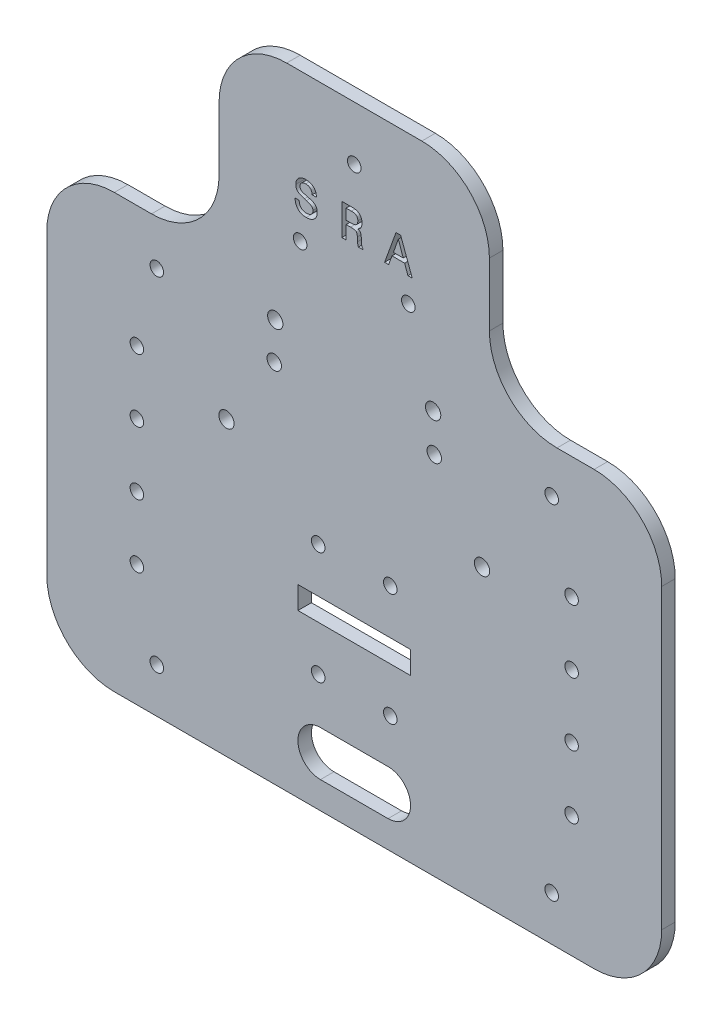
SolidWorks part; units mm, degrees
material "Acrylic (Medium-high impact)"
ref_plane "Front Plane" through (0, 0, 0) normal (0, 0, 1) x (1, 0, 0)
ref_plane "Top Plane" through (0, 0, 0) normal (0, 1, 0) x (1, 0, 0)
ref_plane "Right Plane" through (0, 0, 0) normal (1, 0, 0) x (0, 0, -1)
sketch "Model" plane through (0, 0, 0) normal (0, 0, 1) x (1, 0, 0)
  line L0 (906.1946, 1084.1431) -> (906.1946, 1018.1431)
  line L1 (891.1946, 1003.1431) -> (784.6946, 1003.1431)
  line L2 (845.4446, 1019.1431) -> (830.4446, 1019.1431)
  line L3 (845.4446, 1009.1431) -> (830.4446, 1009.1431)
  line L4 (769.6946, 1084.1431) -> (769.6946, 1018.1431)
  line L5 (891.1946, 1099.1431) -> (882.9446, 1099.1431)
  line L6 (784.6946, 1099.1431) -> (792.9446, 1099.1431)
  line L319 (837.9446, 1143.1431) -> (852.9446, 1143.1431)
  line L320 (837.9446, 1143.1431) -> (852.9446, 1143.1431)
  line L321 (867.9446, 1128.1431) -> (867.9446, 1114.1431)
  line L322 (837.9446, 1143.1431) -> (822.9446, 1143.1431)
  line L323 (807.9446, 1128.1431) -> (807.9446, 1114.1431)
  line L324 (825.4446, 1039.1431) -> (825.4446, 1044.1431)
  line L325 (825.4446, 1044.1431) -> (850.4446, 1044.1431)
  line L326 (850.4446, 1044.1431) -> (850.4446, 1039.1431)
  line L327 (850.4446, 1039.1431) -> (825.4446, 1039.1431)
  circle A0 centre (881.7696, 1013.0631) radius 1.5
  circle A1 centre (794.1196, 1013.0631) radius 1.5
  circle A2 centre (886.1946, 1058.1431) radius 1.5
  circle A3 centre (886.1946, 1044.1431) radius 1.5
  circle A4 centre (789.6946, 1058.1431) radius 1.5
  circle A5 centre (789.6946, 1044.1431) radius 1.5
  circle A6 centre (825.9446, 1110.3585) radius 1.5
  circle A7 centre (849.9446, 1110.3585) radius 1.5
  circle A8 centre (837.9446, 1131.1431) radius 1.5
  circle A9 centre (829.9446, 1054.1431) radius 1.5
  circle A10 centre (845.9446, 1054.1431) radius 1.5
  arc A11 (891.1946, 1003.1431) -> (906.1946, 1018.1431) centre (891.1946, 1018.1431) ccw
  arc A12 (769.6946, 1018.1431) -> (784.6946, 1003.1431) centre (784.6946, 1018.1431) ccw
  arc A13 (850.4446, 1014.1431) -> (845.4446, 1019.1431) centre (845.4446, 1014.1431) ccw
  arc A14 (830.4446, 1019.1431) -> (825.4446, 1014.1431) centre (830.4446, 1014.1431) ccw
  arc A15 (845.4446, 1009.1431) -> (850.4446, 1014.1431) centre (845.4446, 1014.1431) ccw
  arc A16 (825.4446, 1014.1431) -> (830.4446, 1009.1431) centre (830.4446, 1014.1431) ccw
  arc A17 (906.1946, 1084.1431) -> (891.1946, 1099.1431) centre (891.1946, 1084.1431) ccw
  arc A18 (784.6946, 1099.1431) -> (769.6946, 1084.1431) centre (784.6946, 1084.1431) ccw
  arc A19 (867.9446, 1114.1431) -> (882.9446, 1099.1431) centre (882.9446, 1114.1431) ccw
  arc A20 (792.9446, 1099.1431) -> (807.9446, 1114.1431) centre (792.9446, 1114.1431) ccw
  arc A21 (867.9446, 1128.1431) -> (852.9446, 1143.1431) centre (852.9446, 1128.1431) ccw
  arc A22 (822.9446, 1143.1431) -> (807.9446, 1128.1431) centre (822.9446, 1128.1431) ccw
  circle A23 centre (794.1196, 1089.2131) radius 1.5
  circle A24 centre (881.7696, 1089.2876) radius 1.5
  circle A25 centre (820.4131, 1092.5088) radius 1.7
  circle A26 centre (855.4546, 1092.5088) radius 1.7
  circle A27 centre (809.5796, 1067.95) radius 1.7
  circle A28 centre (866.3096, 1067.95) radius 1.7
  circle A29 centre (789.6946, 1072.1431) radius 1.5
  circle A30 centre (789.6946, 1058.1431) radius 1.5
  circle A32 centre (789.6946, 1072.1431) radius 1.5
  circle A33 centre (789.6946, 1086.1431) radius 1.5 [skipped]
  circle A36 centre (886.1946, 1072.1431) radius 1.5
  circle A39 centre (829.9446, 1029.1431) radius 1.5
  circle A40 centre (845.9446, 1029.1431) radius 1.5
  circle A41 centre (789.6946, 1030.1431) radius 1.5
  circle A42 centre (886.1946, 1030.1431) radius 1.5
  dimension "D1" = 3
  dimension "D5" = 24.5588
  dimension "D6" = 20.7846
  dimension "D7" = 12
  dimension "D8" = 64.8069
  dimension "D9" = 2
  dimension "D3" = 2
  dimension "D2" = 2
extrude "Boss-Extrude1" add sketch "Model" along normal blind 3 contours L322 A22 L323 A20 L6 A18 L4 A12 L1 A11 L0 A17 L5 A19 L321 A21 L319 A42 A41 A40 A39 A36 A29 A28 A27 A26 A25 A24 A23 L326 L327 L324 L325 A0 A1
sketch "Sketch2" [suppressed] plane through (0, 0, 3) normal (0, 0, 1) x (1, 0, 0)
  text T0 "SRA"
sketch "Sketch3" plane through (0, 0, 3) normal (0, 0, 1) x (1, 0, 0)
  line L0 (824.2391, 1115.7139) -> (850.725, 1115.7139)
  line L1 (837.9446, 1131.1431) -> (837.4821, 1115.7139)
sketch "Sketch4" plane through (0, 0, 3) normal (0, 0, 1) x (1, 0, 0)
  text T0 "S R A" font "Monospac821 BT" height in points 26
sketch "Sketch5" [suppressed] plane through (0, 0, 3) normal (0, 0, 1) x (1, 0, 0)
extrude "Cut-Extrude1" cut sketch "Sketch4" against normal through all
sketch "Sketch6" plane through (0, 0, 3) normal (0, 0, 1) x (1, 0, 0)
  line L0 (809.5796, 1067.95) -> (809.5796, 1084.26) construction
  line L1 (809.5796, 1084.26) -> (820.1896, 1084.26) construction
  line L2 (866.3096, 1067.95) -> (866.3096, 1084.26) construction
  line L3 (866.3096, 1084.26) -> (855.6996, 1084.26) construction
  circle A0 centre (820.1896, 1084.26) radius 1.6
  circle A1 centre (855.6996, 1084.26) radius 1.6
  dimension "D1" = 16.31
  dimension "D4" = 3.2
  dimension "D5" = 3.2
  dimension "D2" = 10.61
  dimension "D3" = 10.61
extrude "Cut-Extrude2" cut sketch "Sketch6" against normal blind 10
